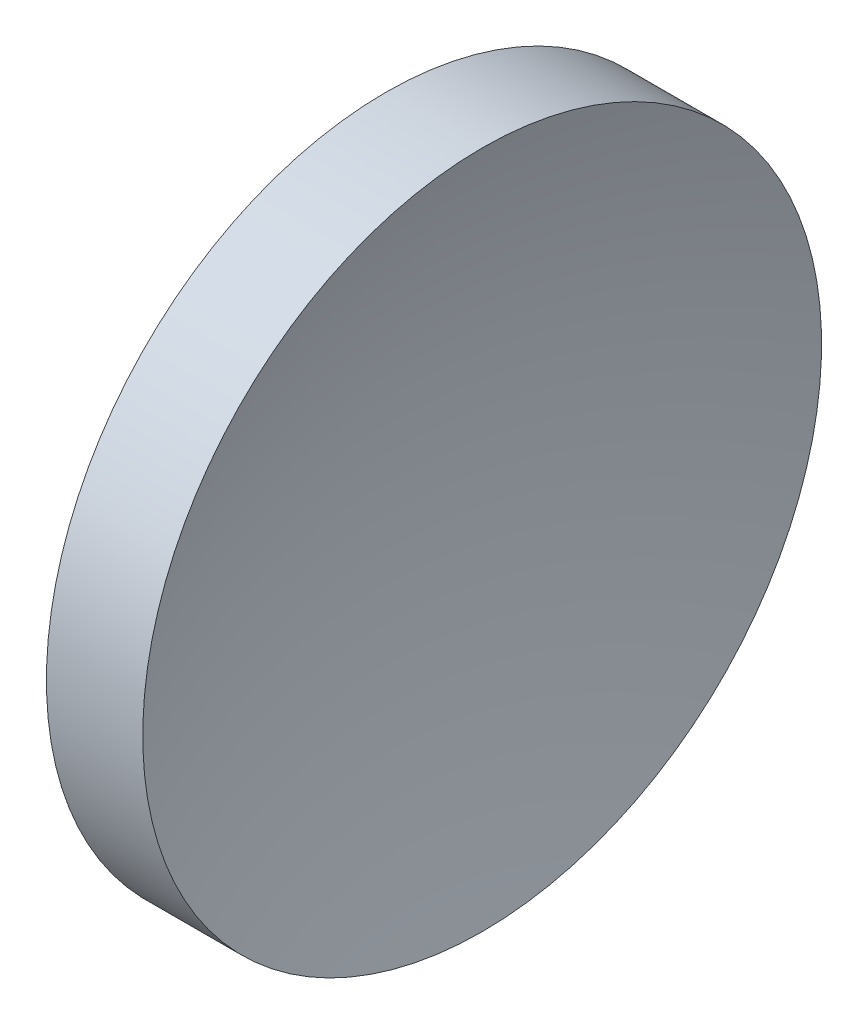
SolidWorks part; units mm, degrees
ref_plane "前视基准面" through (0, 0, 0) normal (0, 0, 1) x (1, 0, 0)
ref_plane "上视基准面" through (0, 0, 0) normal (0, 1, 0) x (1, 0, 0)
ref_plane "右视基准面" through (0, 0, 0) normal (1, 0, 0) x (0, 0, -1)
sketch "草图1" plane through (0, 0, 0) normal (0, 0, 1) x (1, 0, 0)
  line L0 (110.0148, 65.1575) -> (131.4016, 65.1575) construction
  line L1 (114.9754, 65.1575) -> (114.9754, 85.1575)
  line L2 (114.9754, 85.1575) -> (120.652, 85.1575)
  line L3 (117.4754, 65.1575) -> (114.9754, 65.1575)
  arc A0 (120.652, 85.1575) -> (117.4754, 65.1575) centre (182.0254, 65.1575) ccw
revolve "旋转1" add sketch "草图1" angle 360 about L0
